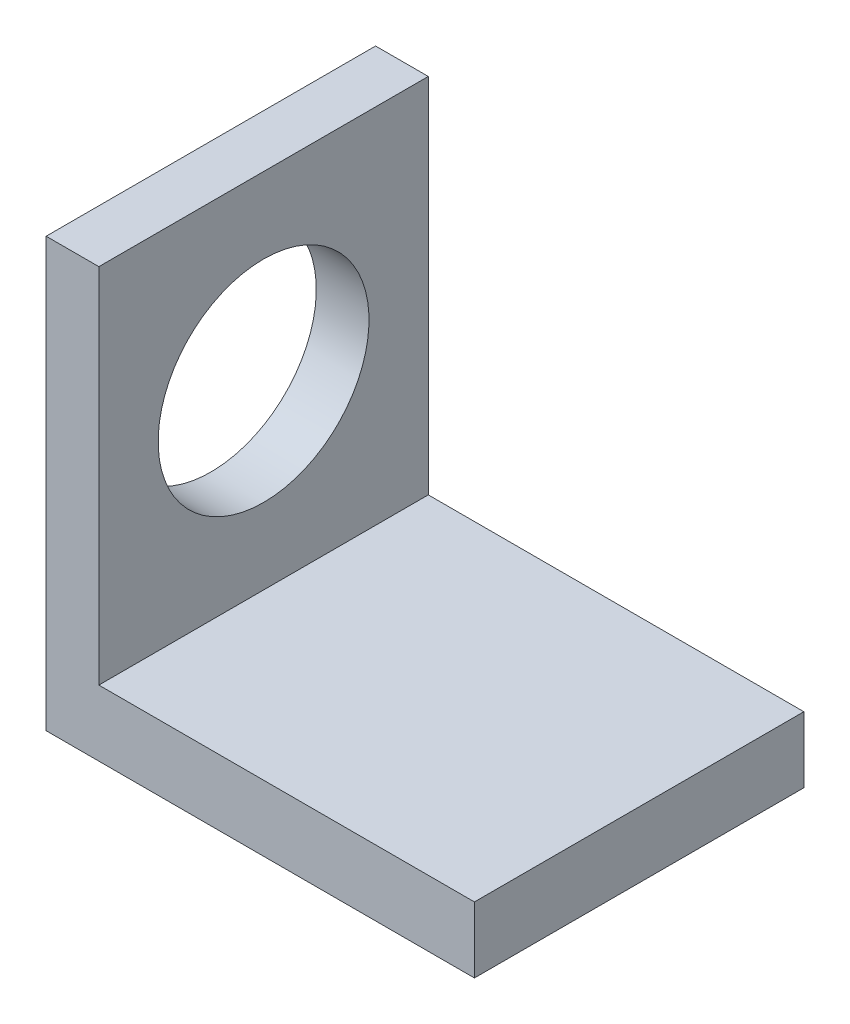
SolidWorks part; units mm, degrees
ref_plane "Ebene vorne" through (0, 0, 0) normal (0, 0, 1) x (1, 0, 0)
ref_plane "Ebene oben" through (0, 0, 0) normal (0, 1, 0) x (1, 0, 0)
ref_plane "Ebene rechts" through (0, 0, 0) normal (1, 0, 0) x (0, 0, -1)
sketch "Skizze1" plane through (0, 0, 0) normal (0, 0, 1) x (1, 0, 0)
  line L0 (0, 65) -> (8, 65)
  line L1 (8, 65) -> (8, 10)
  line L2 (8, 10) -> (65, 10)
  line L3 (65, 10) -> (65, 0)
  line L4 (65, 0) -> (0, 0)
  line L5 (0, 0) -> (0, 65)
  dimension "D1" = 65
  dimension "D2" = 10
  dimension "D3" = 8
  dimension "D4" = 65
extrude "Aufsatz-Linear austragen1" add sketch "Skizze1" against normal blind 50
sketch "Skizze2" plane through (8, 0, 0) normal (1, 0, 0) x (0, 0, -1)
  line L0 (50, 65) -> (0, 65) construction
  line L3 (0, 10) -> (0, 65) construction
  circle A0 centre (25, 37.5) radius 16
  point P6 (0, 39.4885)
  point P7 (50, 37.1269)
  dimension "D1" = 32
  dimension "D2" = 27.5
  dimension "D3" = 25
extrude "Schnitt-Linear austragen1" cut sketch "Skizze2" against normal blind 50
